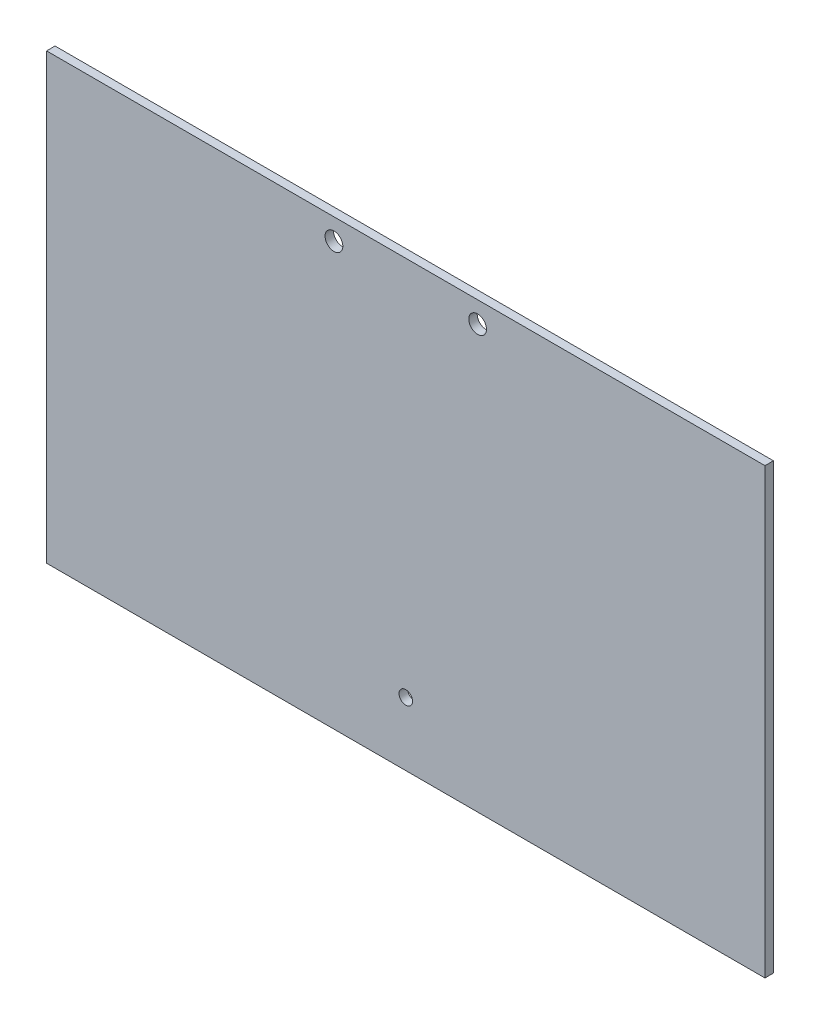
SolidWorks part; units mm, degrees
ref_plane "正面" through (0, 0, 0) normal (0, 0, 1) x (1, 0, 0)
ref_plane "平面" through (0, 0, 0) normal (0, 1, 0) x (1, 0, 0)
ref_plane "右側面" through (0, 0, 0) normal (1, 0, 0) x (0, 0, -1)
sketch "ｽｹｯﾁ1" plane through (0, 0, 0) normal (0, 0, 1) x (1, 0, 0)
  line L1 (-85, 52.5) -> (85, 52.5)
  line L2 (-85, 52.5) -> (-85, -52.5)
  line L3 (-85, -52.5) -> (85, -52.5)
  line L4 (85, 52.5) -> (85, -52.5)
  line L5 (-85, 52.5) -> (85, -52.5) construction
  line L6 (-85, -52.5) -> (85, 52.5) construction
  point P0 (0, 0)
  dimension "D1" = 170
  dimension "D2" = 105
extrude "ﾎﾞｽ - 押し出し1" add sketch "ｽｹｯﾁ1" along normal blind 2
sketch "ｽｹｯﾁ2" plane through (0, 0, 2) normal (0, 0, 1) x (1, 0, 0)
  line L0 (0, -52.5) -> (0, -37.5)
  line L1 (-85, -52.5) -> (85, -52.5) construction
  line L2 (0, 52.5) -> (0, 47.5)
  line L3 (85, 52.5) -> (-85, 52.5) construction
  line L4 (0, 47.5) -> (17, 47.5)
  line L5 (0, 47.5) -> (-17, 47.5)
  circle A0 centre (0, -37.5) radius 1.6
  circle A1 centre (17, 47.5) radius 2.1
  circle A2 centre (-17, 47.5) radius 2.1
  dimension "D2" = 3.2
  dimension "D6" = 4.2
  dimension "D7" = 4.2
  dimension "D1" = 15
  dimension "D3" = 5
  dimension "D4" = 17
  dimension "D5" = 17
extrude "ｶｯﾄ - 押し出し1" cut sketch "ｽｹｯﾁ2" against normal blind 2
